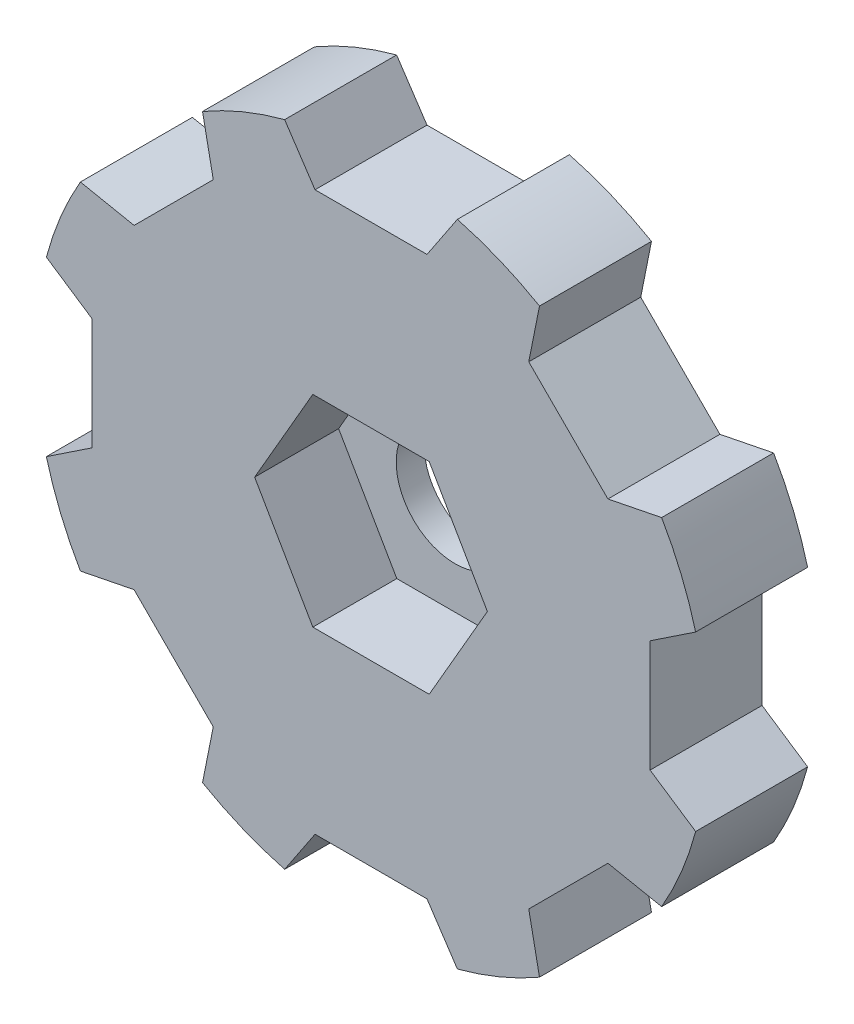
SolidWorks part; units mm, degrees
ref_plane "Front Plane" through (0, 0, 0) normal (0, 0, 1) x (1, 0, 0)
ref_plane "Top Plane" through (0, 0, 0) normal (0, 1, 0) x (1, 0, 0)
ref_plane "Right Plane" through (0, 0, 0) normal (1, 0, 0) x (0, 0, -1)
sketch "Sketch1" plane through (0, 0, 0) normal (0, 0, 1) x (1, 0, 0)
  circle A0 centre (0, 0) radius 2.1
  circle A1 centre (0, 0) radius 12
  dimension "D1" = 4.2
  dimension "D2" = 24
extrude "Boss-Extrude1" add sketch "Sketch1" along normal blind 4
sketch "Sketch2" plane through (0, 0, 4) normal (0, 0, 1) x (1, 0, 0)
  line L1 (4.1569, 0) -> (2.0785, 3.6)
  line L2 (2.0785, 3.6) -> (-2.0785, 3.6)
  line L3 (-2.0785, 3.6) -> (-4.1569, 0)
  line L4 (-4.1569, 0) -> (-2.0785, -3.6)
  line L5 (-2.0785, -3.6) -> (2.0785, -3.6)
  line L6 (2.0785, -3.6) -> (4.1569, 0)
  circle A0 centre (0, 0) radius 3.6 construction
  dimension "D1" = 7.2
extrude "Cut-Extrude1" cut sketch "Sketch2" against normal blind 3
sketch "Sketch3" plane through (0, 0, 4) normal (0, 0, 1) x (1, 0, 0)
  line L0 (9.9689, 2) -> (12.9689, 4)
  line L1 (12.9689, 4) -> (12.9689, -4)
  line L2 (12.9689, -4) -> (9.9689, -2)
  line L3 (9.9689, -2) -> (9.9689, 2)
  line L4 (-14.6433, 0) -> (20.8499, 0) construction
  dimension "D1" = 4
  dimension "D2" = 8
  dimension "D3" = 2
  dimension "D4" = 4
  dimension "D5" = 3
sketch "Sketch4" plane through (0, 0, 0) normal (0, 0, 1) x (1, 0, 0)
  line L0 (0, 14.6497) -> (0, -15.3482) construction
  line L1 (2.2, 0) -> (-2.2, 0) construction
sketch "Sketch5" plane through (0, 0, 0) normal (0, 1, 0) x (1, 0, 0)
  line L0 (0, 7.0615) -> (0, -8.5002) construction
extrude "Cut-Extrude2" cut sketch "Sketch3" against normal up to next (4 mm away)
pattern_circular "CirPattern1" count 8 every 45 about axis through (0, 0, 0) along (0, 0, 1) of "Cut-Extrude2"
